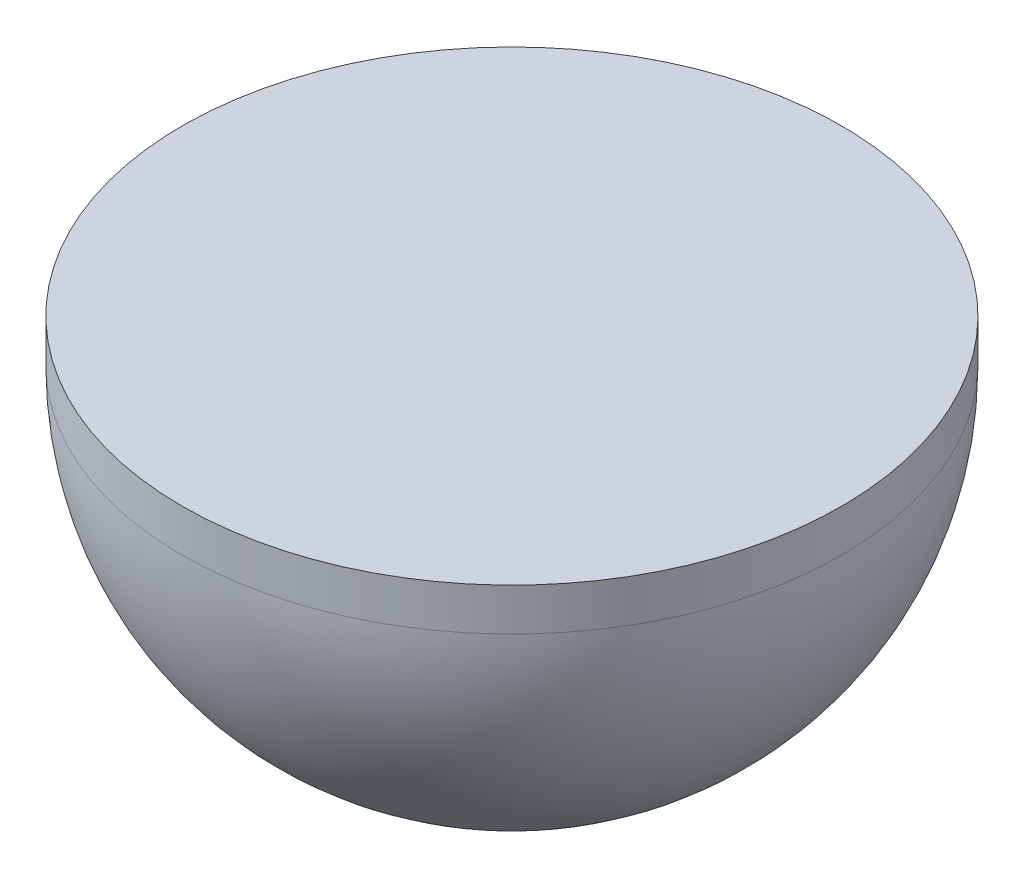
SolidWorks part; units mm, degrees
material "ABS"
ref_plane "Front Plane" through (0, 0, 0) normal (0, 0, 1) x (1, 0, 0)
ref_plane "Top Plane" through (0, 0, 0) normal (0, 1, 0) x (1, 0, 0)
ref_plane "Right Plane" through (0, 0, 0) normal (1, 0, 0) x (0, 0, -1)
sketch "Sketch4" plane through (0, 0, 0) normal (0, 0, 1) x (1, 0, 0)
  line L0 (0, 0) -> (0, 9)
  line L1 (-70, 0) -> (-70, 9)
  line L2 (-70, 9) -> (0, 9)
  line L3 (0, 0) -> (0, -70)
  line L4 (0, 31.6978) -> (0, 19.18) construction
  arc A1 (0, -70) -> (-70, 0) centre (0, 0) cw
revolve "Revolve1" add sketch "Sketch4" angle 360 about L4
